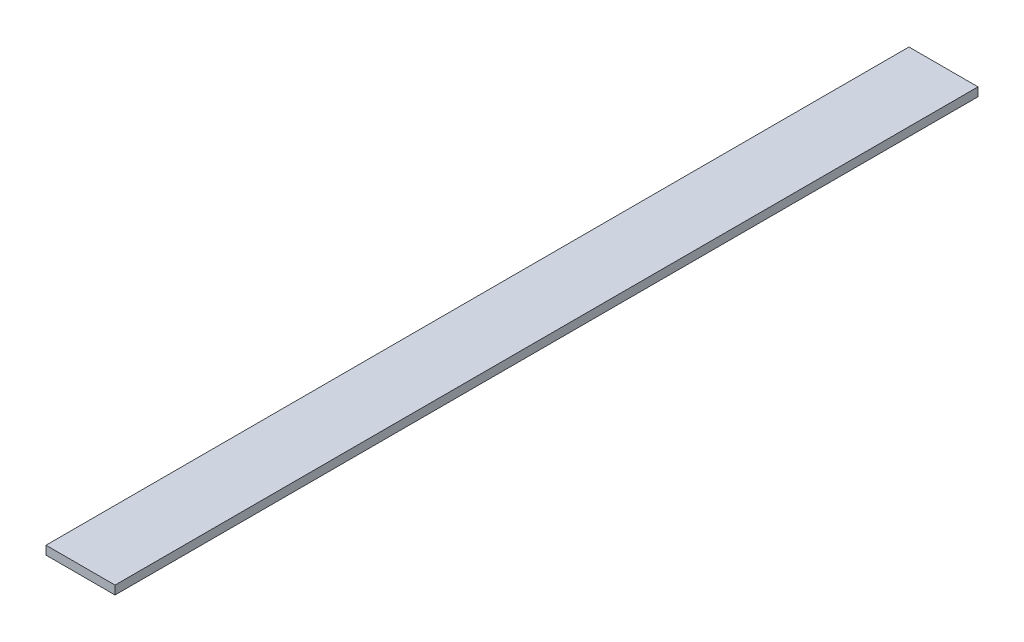
SolidWorks part; units mm, degrees
ref_plane "Plan de face" through (0, 0, 0) normal (0, 0, 1) x (1, 0, 0)
ref_plane "Plan de dessus" through (0, 0, 0) normal (0, 1, 0) x (1, 0, 0)
ref_plane "Plan de droite" through (0, 0, 0) normal (1, 0, 0) x (0, 0, -1)
sketch "Esquisse1" plane through (0, 0, 0) normal (0, 0, 1) x (1, 0, 0)
  line L1 (0, 0) -> (40, 0)
  line L2 (0, 0) -> (0, 5)
  line L3 (0, 5) -> (40, 5)
  line L4 (40, 0) -> (40, 5)
  dimension "D1" = 5
  dimension "D2" = 40
extrude "Boss.-Extru.1" add sketch "Esquisse1" along normal blind 500
